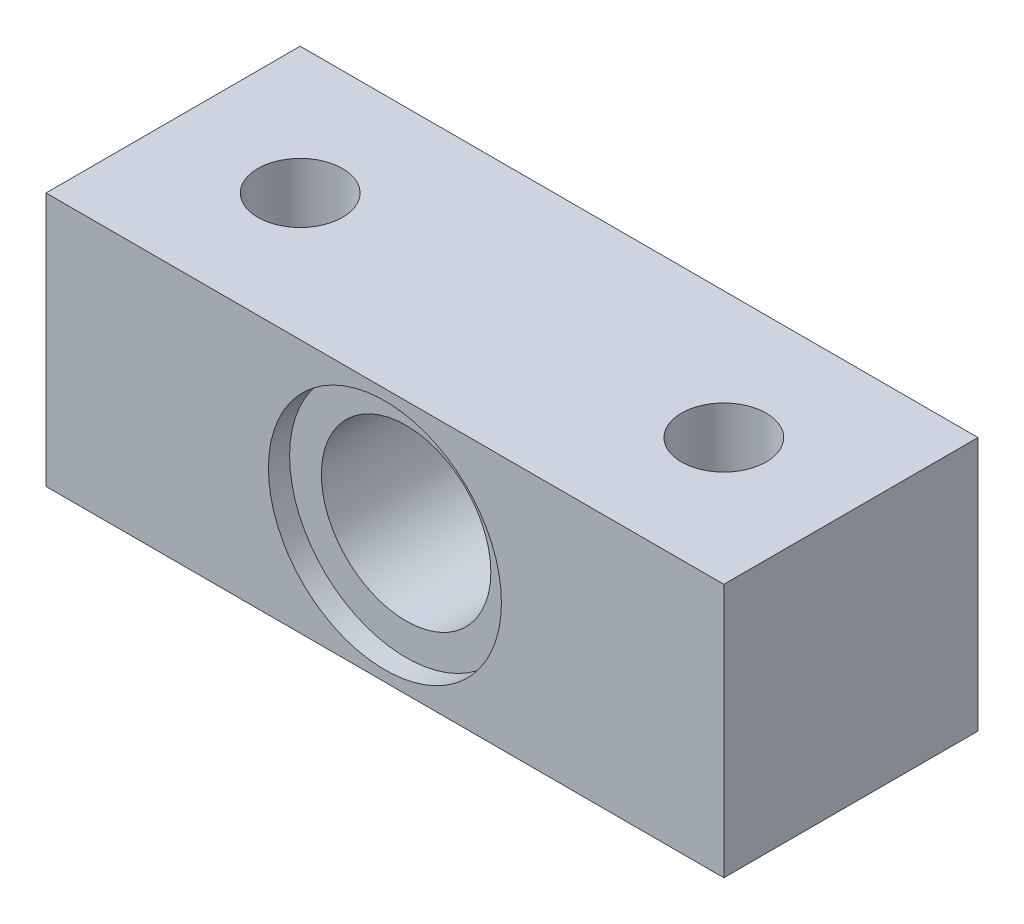
SolidWorks part; units mm, degrees
ref_plane "Front Plane" through (0, 0, 0) normal (0, 0, 1) x (1, 0, 0)
ref_plane "Top Plane" through (0, 0, 0) normal (0, 1, 0) x (1, 0, 0)
ref_plane "Right Plane" through (0, 0, 0) normal (1, 0, 0) x (0, 0, -1)
sketch "Sketch1" plane through (0, 0, 0) normal (0, 0, 1) x (1, 0, 0)
  line L0 (-25.4, 9.525) -> (-25.4, -9.525)
  line L1 (-25.4, -9.525) -> (25.4, -9.525)
  line L2 (25.4, 9.525) -> (25.4, -9.525)
  line L3 (-25.4, 9.525) -> (25.4, 9.525)
  circle A0 centre (0, 0) radius 6.35
extrude "Boss-Extrude1" add sketch "Sketch1" along normal blind 19.05
sketch "Sketch2" plane through (0, 0, 19.05) normal (0, 0, 1) x (1, 0, 0)
  circle A0 centre (0, 0) radius 8.7312
extrude "Cut-Extrude1" cut sketch "Sketch2" against normal blind 1.5875
sketch "Sketch3" plane through (0, -9.525, 0) normal (0, -1, 0) x (1, 0, 0)
  circle A0 centre (-15.875, 9.525) radius 3.175
  circle A1 centre (15.875, 9.525) radius 3.175
extrude "Cut-Extrude2" cut sketch "Sketch3" against normal blind 22.4155
sketch "Sketch4" plane through (0, -9.525, 0) normal (0, -1, 0) x (1, 0, 0)
  circle A0 centre (-15.875, 9.525) radius 4.7625
  circle A1 centre (15.875, 9.525) radius 4.7625
extrude "Cut-Extrude3" cut sketch "Sketch4" against normal blind 6.35
